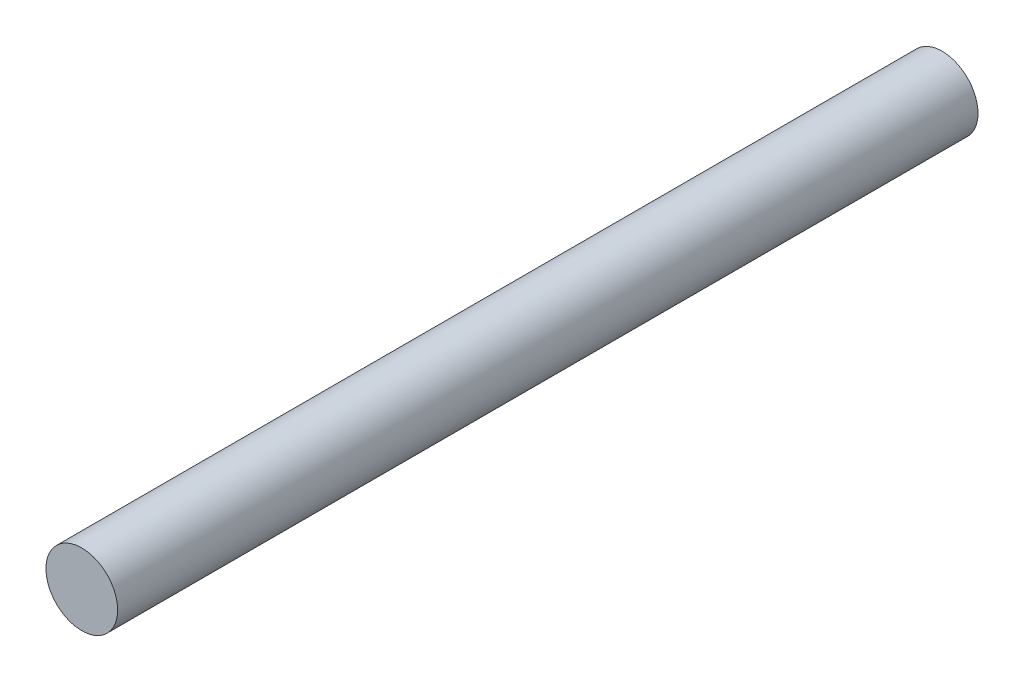
SolidWorks part; units mm, degrees
ref_plane "Front Plane" through (0, 0, 0) normal (0, 0, 1) x (1, 0, 0)
ref_plane "Top Plane" through (0, 0, 0) normal (0, 1, 0) x (1, 0, 0)
ref_plane "Right Plane" through (0, 0, 0) normal (1, 0, 0) x (0, 0, -1)
sketch "Sketch1" plane through (0, 0, 0) normal (0, 0, 1) x (1, 0, 0)
  circle A0 centre (0, 0) radius 3.75
  dimension "D1" = 7.5
extrude "Boss-Extrude1" add sketch "Sketch1" along normal blind 90
